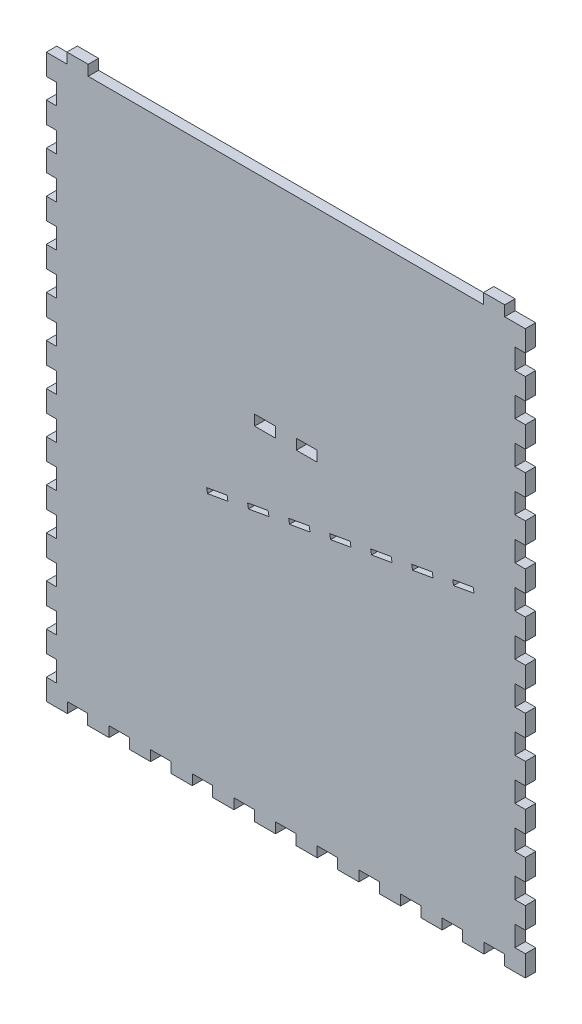
SolidWorks part; units mm, degrees
ref_plane "Front Plane" through (0, 0, 0) normal (0, 0, 1) x (1, 0, 0)
ref_plane "Top Plane" through (0, 0, 0) normal (0, 1, 0) x (1, 0, 0)
ref_plane "Right Plane" through (0, 0, 0) normal (1, 0, 0) x (0, 0, -1)
sketch "Sketch1" plane through (0, 0, 0) normal (0, 0, 1) x (1, 0, 0)
  line L0 (0, 0) -> (12.573, 0)
  line L1 (12.573, 0) -> (12.573, 6.35)
  line L2 (12.573, 6.35) -> (25.527, 6.35)
  line L3 (25.527, 6.35) -> (25.527, 0)
  line L4 (25.527, 0) -> (266.573, 0)
  line L5 (266.573, 0) -> (266.573, 6.35)
  line L6 (266.573, 6.35) -> (279.527, 6.35)
  line L7 (279.527, 6.35) -> (279.527, 0)
  line L8 (279.527, 0) -> (292.1, 0)
  line L9 (0, -12.827) -> (0, 0)
  line L10 (0, -12.827) -> (6.35, -12.827)
  line L11 (6.35, -12.827) -> (6.35, -25.273)
  line L12 (6.35, -25.273) -> (0, -25.273)
  line L13 (0, -25.273) -> (0, -38.227)
  line L14 (0, -38.227) -> (6.35, -38.227)
  line L15 (6.35, -38.227) -> (6.35, -50.673)
  line L16 (6.35, -50.673) -> (0, -50.673)
  line L17 (0, -50.673) -> (0, -63.627)
  line L18 (0, -63.627) -> (6.35, -63.627)
  line L19 (6.35, -63.627) -> (6.35, -76.073)
  line L20 (6.35, -76.073) -> (0, -76.073)
  line L21 (0, -76.073) -> (0, -89.027)
  line L22 (0, -89.027) -> (6.35, -89.027)
  line L23 (6.35, -89.027) -> (6.35, -101.473)
  line L24 (6.35, -101.473) -> (0, -101.473)
  line L25 (0, -101.473) -> (0, -114.427)
  line L26 (0, -114.427) -> (6.35, -114.427)
  line L27 (6.35, -114.427) -> (6.35, -126.873)
  line L28 (6.35, -126.873) -> (0, -126.873)
  line L29 (0, -126.873) -> (0, -139.827)
  line L30 (0, -139.827) -> (6.35, -139.827)
  line L31 (6.35, -139.827) -> (6.35, -152.273)
  line L32 (6.35, -152.273) -> (0, -152.273)
  line L33 (0, -152.273) -> (0, -165.227)
  line L34 (0, -165.227) -> (6.35, -165.227)
  line L35 (6.35, -165.227) -> (6.35, -177.673)
  line L36 (6.35, -177.673) -> (0, -177.673)
  line L37 (0, -177.673) -> (0, -190.627)
  line L38 (0, -190.627) -> (6.35, -190.627)
  line L39 (6.35, -190.627) -> (6.35, -203.073)
  line L40 (6.35, -203.073) -> (0, -203.073)
  line L41 (0, -203.073) -> (0, -216.027)
  line L42 (0, -216.027) -> (6.35, -216.027)
  line L43 (6.35, -216.027) -> (6.35, -228.473)
  line L44 (6.35, -228.473) -> (0, -228.473)
  line L45 (0, -228.473) -> (0, -241.427)
  line L46 (0, -241.427) -> (6.35, -241.427)
  line L47 (6.35, -241.427) -> (6.35, -253.873)
  line L48 (6.35, -253.873) -> (0, -253.873)
  line L49 (0, -253.873) -> (0, -266.827)
  line L50 (0, -266.827) -> (6.35, -266.827)
  line L51 (6.35, -266.827) -> (6.35, -279.273)
  line L52 (6.35, -279.273) -> (0, -279.273)
  line L53 (292.1, 0) -> (292.1, -12.827)
  line L54 (292.1, -12.827) -> (285.75, -12.827)
  line L55 (285.75, -12.827) -> (285.75, -25.273)
  line L56 (285.75, -25.273) -> (292.1, -25.273)
  line L57 (292.1, -25.273) -> (292.1, -38.227)
  line L58 (292.1, -38.227) -> (285.75, -38.227)
  line L59 (0, -342.9) -> (12.827, -342.9)
  line L60 (12.827, -342.9) -> (12.827, -336.55)
  line L61 (12.827, -336.55) -> (25.273, -336.55)
  line L62 (25.273, -336.55) -> (25.273, -342.9)
  line L63 (25.273, -342.9) -> (38.227, -342.9)
  line L64 (38.227, -342.9) -> (38.227, -336.55)
  line L65 (38.227, -336.55) -> (50.673, -336.55)
  line L66 (50.673, -336.55) -> (50.673, -342.9)
  line L67 (50.673, -342.9) -> (63.627, -342.9)
  line L68 (63.627, -342.9) -> (63.627, -336.55)
  line L69 (63.627, -336.55) -> (76.073, -336.55)
  line L70 (76.073, -336.55) -> (76.073, -342.9)
  line L71 (76.073, -342.9) -> (89.027, -342.9)
  line L72 (89.027, -342.9) -> (89.027, -336.55)
  line L73 (89.027, -336.55) -> (101.473, -336.55)
  line L74 (101.473, -336.55) -> (101.473, -342.9)
  line L75 (101.473, -342.9) -> (114.427, -342.9)
  line L76 (114.427, -342.9) -> (114.427, -336.55)
  line L77 (114.427, -336.55) -> (126.873, -336.55)
  line L78 (126.873, -336.55) -> (126.873, -342.9)
  line L79 (126.873, -342.9) -> (139.827, -342.9)
  line L80 (139.827, -342.9) -> (139.827, -336.55)
  line L81 (139.827, -336.55) -> (152.273, -336.55)
  line L82 (152.273, -336.55) -> (152.273, -342.9)
  line L83 (152.273, -342.9) -> (165.227, -342.9)
  line L84 (165.227, -342.9) -> (165.227, -336.55)
  line L85 (165.227, -336.55) -> (177.673, -336.55)
  line L86 (177.673, -336.55) -> (177.673, -342.9)
  line L87 (177.673, -342.9) -> (190.627, -342.9)
  line L88 (190.627, -342.9) -> (190.627, -336.55)
  line L89 (190.627, -336.55) -> (203.073, -336.55)
  line L90 (203.073, -336.55) -> (203.073, -342.9)
  line L91 (203.073, -342.9) -> (216.027, -342.9)
  line L92 (216.027, -342.9) -> (216.027, -336.55)
  line L93 (216.027, -336.55) -> (228.473, -336.55)
  line L94 (228.473, -336.55) -> (228.473, -342.9)
  line L95 (228.473, -342.9) -> (241.427, -342.9)
  line L96 (241.427, -342.9) -> (241.427, -336.55)
  line L97 (241.427, -336.55) -> (253.873, -336.55)
  line L98 (253.873, -336.55) -> (253.873, -342.9)
  line L99 (253.873, -342.9) -> (266.827, -342.9)
  line L100 (266.827, -342.9) -> (266.827, -336.55)
  line L101 (266.827, -336.55) -> (279.273, -336.55)
  line L102 (279.273, -336.55) -> (279.273, -342.9)
  line L103 (285.75, -38.227) -> (285.75, -50.673)
  line L104 (285.75, -50.673) -> (292.1, -50.673)
  line L105 (292.1, -50.673) -> (292.1, -63.627)
  line L106 (292.1, -63.627) -> (285.75, -63.627)
  line L107 (292.1, -342.9) -> (279.273, -342.9)
  line L108 (285.75, -63.627) -> (285.75, -76.073)
  line L109 (285.75, -76.073) -> (292.1, -76.073)
  line L110 (292.1, -76.073) -> (292.1, -89.027)
  line L111 (292.1, -89.027) -> (285.75, -89.027)
  line L112 (285.75, -89.027) -> (285.75, -101.473)
  line L113 (285.75, -101.473) -> (292.1, -101.473)
  line L114 (292.1, -101.473) -> (292.1, -114.427)
  line L115 (292.1, -114.427) -> (285.75, -114.427)
  line L116 (285.75, -114.427) -> (285.75, -126.873)
  line L117 (285.75, -126.873) -> (292.1, -126.873)
  line L118 (292.1, -126.873) -> (292.1, -139.827)
  line L119 (292.1, -139.827) -> (285.75, -139.827)
  line L120 (285.75, -139.827) -> (285.75, -152.273)
  line L121 (285.75, -152.273) -> (292.1, -152.273)
  line L122 (292.1, -152.273) -> (292.1, -165.227)
  line L123 (292.1, -165.227) -> (285.75, -165.227)
  line L124 (285.75, -165.227) -> (285.75, -177.673)
  line L125 (285.75, -177.673) -> (292.1, -177.673)
  line L126 (292.1, -177.673) -> (292.1, -190.627)
  line L127 (292.1, -190.627) -> (285.75, -190.627)
  line L128 (285.75, -190.627) -> (285.75, -203.073)
  line L129 (285.75, -203.073) -> (292.1, -203.073)
  line L130 (292.1, -203.073) -> (292.1, -216.027)
  line L131 (292.1, -216.027) -> (285.75, -216.027)
  line L132 (285.75, -216.027) -> (285.75, -228.473)
  line L133 (285.75, -228.473) -> (292.1, -228.473)
  line L134 (292.1, -228.473) -> (292.1, -241.427)
  line L135 (292.1, -241.427) -> (285.75, -241.427)
  line L136 (285.75, -241.427) -> (285.75, -253.873)
  line L137 (285.75, -253.873) -> (292.1, -253.873)
  line L138 (292.1, -253.873) -> (292.1, -266.827)
  line L139 (292.1, -266.827) -> (285.75, -266.827)
  line L140 (285.75, -266.827) -> (285.75, -279.273)
  line L141 (285.75, -279.273) -> (292.1, -279.273)
  line L142 (292.1, -279.273) -> (292.1, -292.227)
  line L143 (146.05, 0) -> (146.05, -285.75) construction
  line L144 (0, -279.273) -> (0, -292.227)
  line L145 (0, -292.227) -> (6.35, -292.227)
  line L146 (6.35, -292.227) -> (6.35, -304.673)
  line L147 (6.35, -304.673) -> (0, -304.673)
  line L148 (0, -304.673) -> (0, -317.627)
  line L149 (0, -317.627) -> (6.35, -317.627)
  line L150 (6.35, -317.627) -> (6.35, -330.073)
  line L151 (6.35, -330.073) -> (0, -330.073)
  line L152 (260.8705, -155.3517) -> (248.3634, -157.557)
  line L153 (260.8705, -155.3517) -> (260.35, -152.4)
  line L154 (248.3634, -157.557) -> (247.8429, -154.6053)
  line L155 (260.35, -152.4) -> (247.8429, -154.6053)
  line L156 (235.8563, -159.7623) -> (223.3493, -161.9677)
  line L157 (235.8563, -159.7623) -> (235.3359, -156.8107)
  line L158 (223.3493, -161.9677) -> (222.8288, -159.016)
  line L159 (235.3359, -156.8107) -> (222.8288, -159.016)
  line L160 (152.4635, -127.635) -> (152.4635, -133.985)
  line L161 (127.0635, -127.635) -> (139.6365, -127.635)
  line L162 (127.0635, -127.635) -> (127.0635, -133.985)
  line L163 (127.0635, -133.985) -> (139.6365, -133.985)
  line L164 (139.6365, -127.635) -> (139.6365, -133.985)
  line L165 (165.0365, -133.985) -> (152.4635, -133.985)
  line L166 (165.0365, -127.635) -> (165.0365, -133.985)
  line L167 (165.0365, -127.635) -> (152.4635, -127.635)
  line L168 (210.8422, -164.173) -> (198.3352, -166.3783)
  line L169 (210.8422, -164.173) -> (210.3218, -161.2213)
  line L170 (198.3352, -166.3783) -> (197.8147, -163.4267)
  line L171 (210.3218, -161.2213) -> (197.8147, -163.4267)
  line L172 (185.8281, -168.5837) -> (173.321, -170.789)
  line L173 (0, -330.073) -> (0, -342.9)
  line L174 (292.1, -292.227) -> (285.75, -292.227)
  line L175 (285.75, -292.227) -> (285.75, -304.673)
  line L176 (285.75, -304.673) -> (292.1, -304.673)
  line L177 (292.1, -304.673) -> (292.1, -317.627)
  line L178 (292.1, -317.627) -> (285.75, -317.627)
  line L179 (285.75, -317.627) -> (285.75, -330.073)
  line L180 (285.75, -330.073) -> (292.1, -330.073)
  line L181 (185.8281, -168.5837) -> (185.3076, -165.632)
  line L182 (173.321, -170.789) -> (172.8006, -167.8373)
  line L183 (185.3076, -165.632) -> (172.8006, -167.8373)
  line L184 (160.814, -172.9943) -> (148.3069, -175.1997)
  line L185 (160.814, -172.9943) -> (160.2935, -170.0427)
  line L186 (148.3069, -175.1997) -> (147.7865, -172.248)
  line L187 (160.2935, -170.0427) -> (147.7865, -172.248)
  line L188 (135.7999, -177.405) -> (123.2928, -179.6103)
  line L189 (135.7999, -177.405) -> (135.2794, -174.4533)
  line L190 (123.2928, -179.6103) -> (122.7724, -176.6587)
  line L191 (135.2794, -174.4533) -> (122.7724, -176.6587)
  line L192 (110.7858, -181.8156) -> (98.2787, -184.021)
  line L193 (292.1, -330.073) -> (292.1, -342.9)
  line L194 (110.7858, -181.8156) -> (110.2653, -178.864)
  line L195 (98.2787, -184.021) -> (97.7582, -181.0693)
  line L196 (110.2653, -178.864) -> (97.7582, -181.0693)
  line L197 (279.273, -342.9) -> (292.227, -342.9) [skipped]
  line L198 (292.1, -330.073) -> (292.1, -343.027) [skipped]
  line L199 (0, -330.073) -> (0, -343.027) [skipped]
  line L200 (6.35, -330.073) -> (0, -330.073) [skipped]
  dimension "D2" = 12.954
  dimension "D3" = 6.35
  dimension "D4" = 6.35
  dimension "D5" = 12.573
  dimension "D6" = 12.954
  dimension "D7" = 12.573
  dimension "D8" = 12.827
  dimension "D9" = 12.446
  dimension "D10" = 6.35
  dimension "D11" = 6.35
  dimension "D12" = 12.954
  dimension "D14" = 12.827
  dimension "D15" = 12.827
  dimension "D16" = 12.446
  dimension "D17" = 12.954
  dimension "D18" = 6.35
  dimension "D19" = 6.35
  dimension "D21" = 12.446
  dimension "D22" = 12.954
  dimension "D23" = 6.35
  dimension "D24" = 6.35
  dimension "D25" = 13
  dimension "D27" = 12.827
  dimension "D28" = 127.635
  dimension "D29" = 12.573
  dimension "D30" = 6.35
  dimension "D31" = 241.046
  dimension "D32" = 12.7
  dimension "D33" = 10
  dimension "D34" = 6.4135
  dimension "D26" = 2.9972
  dimension "D36" = 152.4
  dimension "D37" = 25.4
  dimension "D13" = 13
  dimension "D20" = 11
extrude "Boss-Extrude1" add sketch "Sketch1" along normal blind 6.35
